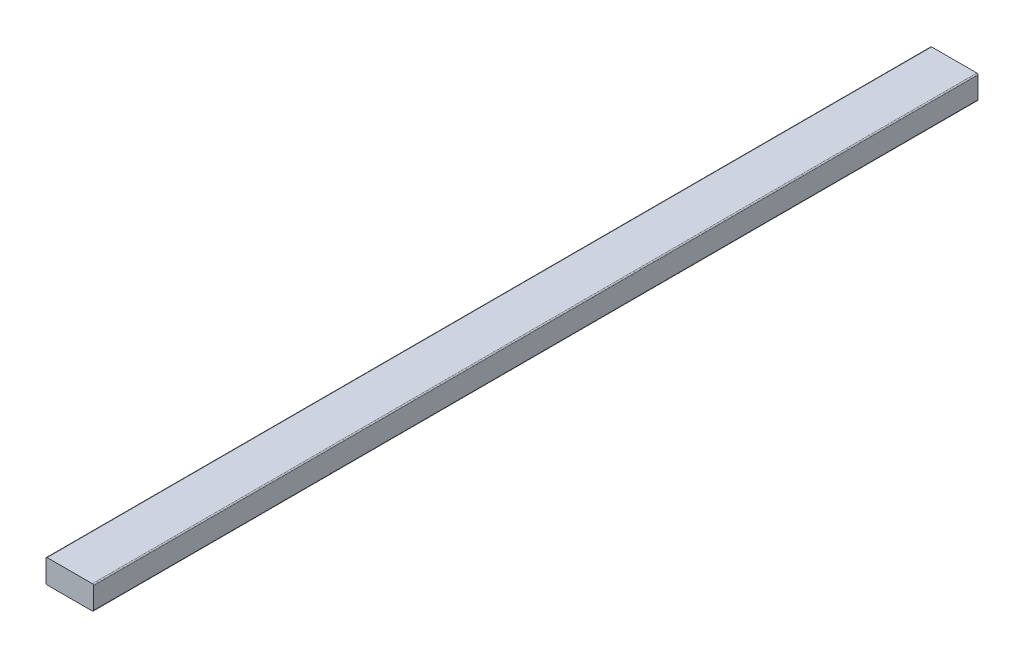
SolidWorks part; units mm, degrees
ref_plane "Front Plane" through (0, 0, 0) normal (0, 0, 1) x (1, 0, 0)
ref_plane "Top Plane" through (0, 0, 0) normal (0, 1, 0) x (1, 0, 0)
ref_plane "Right Plane" through (0, 0, 0) normal (1, 0, 0) x (0, 0, -1)
sketch "Sketch1" plane through (0, 0, 0) normal (0, 0, 1) x (1, 0, 0)
  line L1 (-20, -10) -> (20, -10)
  line L2 (-20, -10) -> (-20, 10)
  line L3 (-20, 10) -> (20, 10)
  line L4 (20, -10) -> (20, 10)
  line L5 (-20, -10) -> (20, 10) construction
  line L6 (-20, 10) -> (20, -10) construction
  point P0 (0, 0)
  dimension "D1" = 20
  dimension "D2" = 40
extrude "Boss-Extrude1" add sketch "Sketch1" along normal blind 745
fillet "Fillet1" radius 1 4 edges at (20, -10, 372.5) (-20, -10, 372.5) (-20, 10, 372.5) (20, 10, 372.5)
